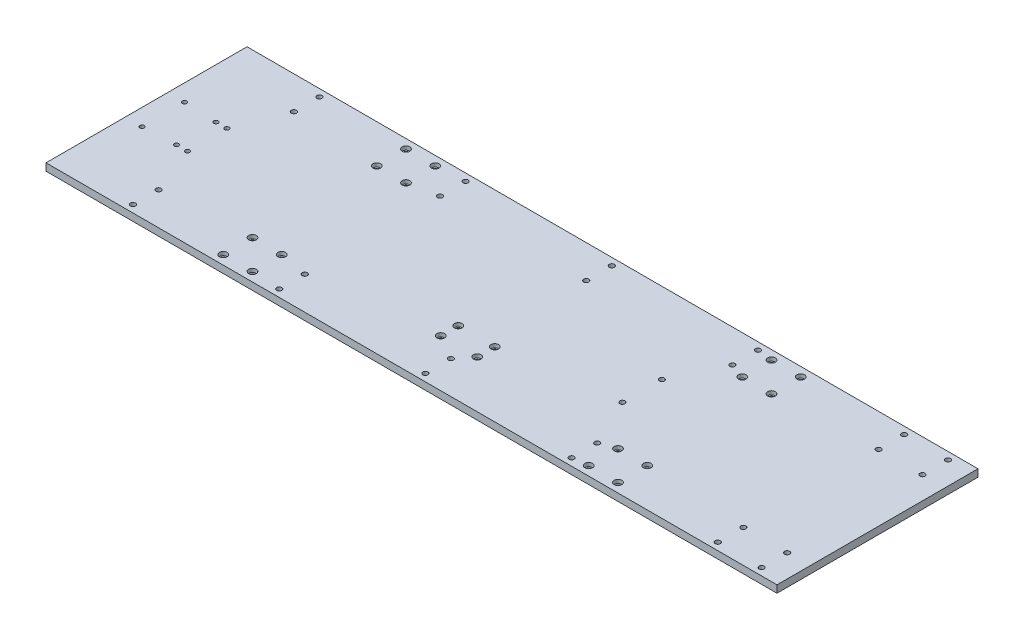
SolidWorks part; units mm, degrees
ref_plane "Спереди" through (0, 0, 0) normal (0, 0, 1) x (1, 0, 0)
ref_plane "Сверху" through (0, 0, 0) normal (0, 1, 0) x (1, 0, 0)
ref_plane "Справа" through (0, 0, 0) normal (1, 0, 0) x (0, 0, -1)
sketch "Эскиз1" plane through (0, 0, 0) normal (0, 1, 0) x (1, 0, 0)
  line L0 (-276.7974, 6.2908) -> (-314.5425, 6.2908) construction
  line L1 (-276.7974, 143.7908) -> (723.2026, 143.7908)
  line L2 (-276.7974, 143.7908) -> (-276.7974, -131.2092)
  line L3 (-276.7974, -131.2092) -> (723.2026, -131.2092)
  line L4 (723.2026, 143.7908) -> (723.2026, -131.2092)
  line L5 (223.2026, 187.065) -> (223.2026, 256.4984) construction
  line L6 (-208.7974, 33.2908) -> (-193.7974, 33.2908) construction
  line L7 (-224.8434, 116.2908) -> (-167.7974, 116.2908) construction
  line L8 (-167.7974, 133.7908) -> (32.2026, 133.7908) construction
  line L9 (632.2026, 133.7908) -> (692.2026, 133.7908) construction
  line L10 (-26.7974, -64.8503) -> (-26.7974, -110.3228) construction
  line L11 (473.2026, -51.2561) -> (473.2026, -110.7998) construction
  line L12 (-46.7974, -118.7092) -> (-46.7974, -78.7092) construction
  line L13 (493.2026, -118.7092) -> (493.2026, -78.7092) construction
  line L14 (198.2026, -66.2092) -> (198.2026, -42.2092) construction
  circle A0 centre (-253.7974, 35.2908) radius 3
  circle A1 centre (-208.7974, 33.2908) radius 3
  circle A2 centre (-193.7974, 33.2908) radius 3
  circle A3 centre (-167.7974, 133.7908) radius 3.5
  circle A4 centre (32.2026, 133.7908) radius 3.5
  circle A5 centre (232.2026, 133.7908) radius 3.5
  circle A6 centre (432.2026, 133.7908) radius 3.5
  circle A7 centre (632.2026, 133.7908) radius 3.5
  circle A8 centre (692.2026, 133.7908) radius 3.5
  circle A9 centre (692.2026, 98.7908) radius 3.5
  circle A10 centre (632.2026, 98.7908) radius 3.5
  circle A11 centre (432.2026, 98.7908) radius 3.5
  circle A12 centre (232.2026, 98.7908) radius 3.5
  circle A13 centre (32.2026, 98.7908) radius 3.5
  circle A14 centre (-167.7974, 98.7908) radius 3.5
  circle A15 centre (632.2026, -86.2092) radius 3.5
  circle A16 centre (692.2026, -86.2092) radius 3.5
  circle A17 centre (692.2026, -121.2092) radius 3.5
  circle A18 centre (632.2026, -121.2092) radius 3.5
  circle A19 centre (432.2026, -86.2092) radius 3.5
  circle A20 centre (432.2026, -121.2092) radius 3.5
  circle A21 centre (232.2026, -86.2092) radius 3.5
  circle A22 centre (232.2026, -121.2092) radius 3.5
  circle A23 centre (32.2026, -86.2092) radius 3.5
  circle A24 centre (32.2026, -121.2092) radius 3.5
  circle A25 centre (-167.7974, -86.2092) radius 3.5
  circle A26 centre (-167.7974, -121.2092) radius 3.5
  circle A27 centre (401.2026, 33.2908) radius 3.5
  circle A28 centre (401.2026, -20.7092) radius 3.5
  circle A29 centre (-193.7974, -20.7092) radius 3
  circle A30 centre (-208.7974, -20.7092) radius 3
  circle A31 centre (-253.7974, -22.7092) radius 3
  circle A32 centre (-46.7974, -118.7092) radius 3.2
  circle A33 centre (-46.7974, -78.7092) radius 3.2
  circle A34 centre (-6.7974, -78.7092) radius 3.2
  circle A35 centre (-6.7974, -118.7092) radius 3.2
  circle A36 centre (-6.7974, 131.2908) radius 3.2
  circle A37 centre (-46.7974, 131.2908) radius 3.2
  circle A38 centre (-6.7974, 91.2908) radius 3.2
  circle A39 centre (-46.7974, 91.2908) radius 3.2
  circle A40 centre (493.2026, -118.7092) radius 3.2
  circle A41 centre (493.2026, -78.7092) radius 3.2
  circle A42 centre (453.2026, -118.7092) radius 3.2
  circle A43 centre (453.2026, -78.7092) radius 3.2
  circle A44 centre (493.2026, 131.2908) radius 3.2
  circle A45 centre (453.2026, 131.2908) radius 3.2
  circle A46 centre (493.2026, 91.2908) radius 3.2
  circle A47 centre (453.2026, 91.2908) radius 3.2
  circle A48 centre (198.2026, -66.2092) radius 3.2
  circle A49 centre (198.2026, -42.2092) radius 3.2
  circle A50 centre (248.2026, -66.2092) radius 3.2
  circle A51 centre (248.2026, -42.2092) radius 3.2
  dimension "D3" = 6
  dimension "D10" = 7
  dimension "D18" = 7
  dimension "D22" = 6.4
  dimension "D27" = 6.4
  dimension "D1" = 137.5
  dimension "D2" = 137.5
  dimension "D4" = 23
  dimension "D5" = 29
  dimension "D7" = 25
  dimension "D9" = 15
  dimension "D11" = 10
  dimension "D12" = 109
  dimension "D13" = 17.5
  dimension "D15" = 200
  dimension "D16" = 60
  dimension "D19" = 27
  dimension "D20" = 250
  dimension "D21" = 250
  dimension "D23" = 12.5
  dimension "D25" = 40
  dimension "D26" = 20
  dimension "D28" = 12.5
  dimension "D29" = 20
  dimension "D31" = 40
  dimension "D32" = 678
  dimension "D6" = 250
  dimension "D33" = 65
  dimension "D35" = 24
  dimension "D8" = 2
  dimension "D14" = 5
  dimension "D17" = 2
  dimension "D24" = 2
  dimension "D30" = 2
  dimension "D34" = 2
extrude "Бобышка-Вытянуть1" add sketch "Эскиз1" along normal blind 10
sketch "вырез под шляпки" plane through (0, 10, -10) normal (0, -1, 0) x (1, 0, 0)
  line L0 (-276.7974, 3.7092) -> (-314.5425, 3.7092) construction
  line L1 (-276.7974, 141.2092) -> (723.2026, 141.2092)
  line L2 (-276.7974, 141.2092) -> (-276.7974, -133.7908)
  line L4 (723.2026, 141.2092) -> (723.2026, -133.7908)
  line L7 (-224.8434, 113.7092) -> (-167.7974, 113.7092) construction
  line L10 (-26.7974, -55.5159) -> (-26.7974, -100.9885) construction
  line L11 (473.2026, -51.2561) -> (473.2026, -110.7998) construction
  line L12 (-46.7974, -121.2908) -> (-46.7974, -81.2908) construction
  line L13 (493.2026, -121.2908) -> (493.2026, -81.2908) construction
  line L14 (-276.7974, 141.2092) -> (723.2026, 141.2092) construction
  circle A32 centre (-46.7974, -121.2908) radius 5.25
  circle A33 centre (-46.7974, -81.2908) radius 5.25
  circle A34 centre (-6.7974, -81.2908) radius 5.25
  circle A35 centre (-6.7974, -121.2908) radius 5.25
  circle A36 centre (-6.7974, 128.7092) radius 5.25
  circle A37 centre (-46.7974, 128.7092) radius 5.25
  circle A38 centre (-6.7974, 88.7092) radius 5.25
  circle A39 centre (-46.7974, 88.7092) radius 5.25
  circle A40 centre (493.2026, -121.2908) radius 5.25
  circle A41 centre (493.2026, -81.2908) radius 5.25
  circle A42 centre (453.2026, -121.2908) radius 5.25
  circle A43 centre (453.2026, -81.2908) radius 5.25
  circle A44 centre (493.2026, 128.7092) radius 5.25
  circle A45 centre (453.2026, 128.7092) radius 5.25
  circle A46 centre (493.2026, 88.7092) radius 5.25
  circle A47 centre (453.2026, 88.7092) radius 5.25
  circle A48 centre (198.2026, 52.2092) radius 5.25
  circle A49 centre (198.2026, 76.2092) radius 5.25
  circle A50 centre (248.2026, 76.2092) radius 5.25
  circle A51 centre (248.2026, 52.2092) radius 5.25
  point P8 (198.2026, 52.2092)
  point P11 (198.2026, 76.2092)
  point P14 (248.2026, 76.2092)
  point P17 (248.2026, 52.2092)
  dimension "D22" = 10.5
  dimension "D27" = 10.5
  dimension "D1" = 137.5
  dimension "D20" = 250
  dimension "D21" = 250
  dimension "D25" = 40
  dimension "D26" = 20
  dimension "D29" = 20
  dimension "D31" = 40
  dimension "D32" = 137.5
  dimension "D24" = 2
  dimension "D30" = 2
extrude "Вырез-Вытянуть1" cut sketch "вырез под шляпки" along normal blind 5 contours A32 | A35 | A33 | A34 | A39 | A38 | A37 | A36 | A45 | A47 | A43 | A42 | A40 | A41 | A46 | A44 | A49 | A48 | A51 | A50
